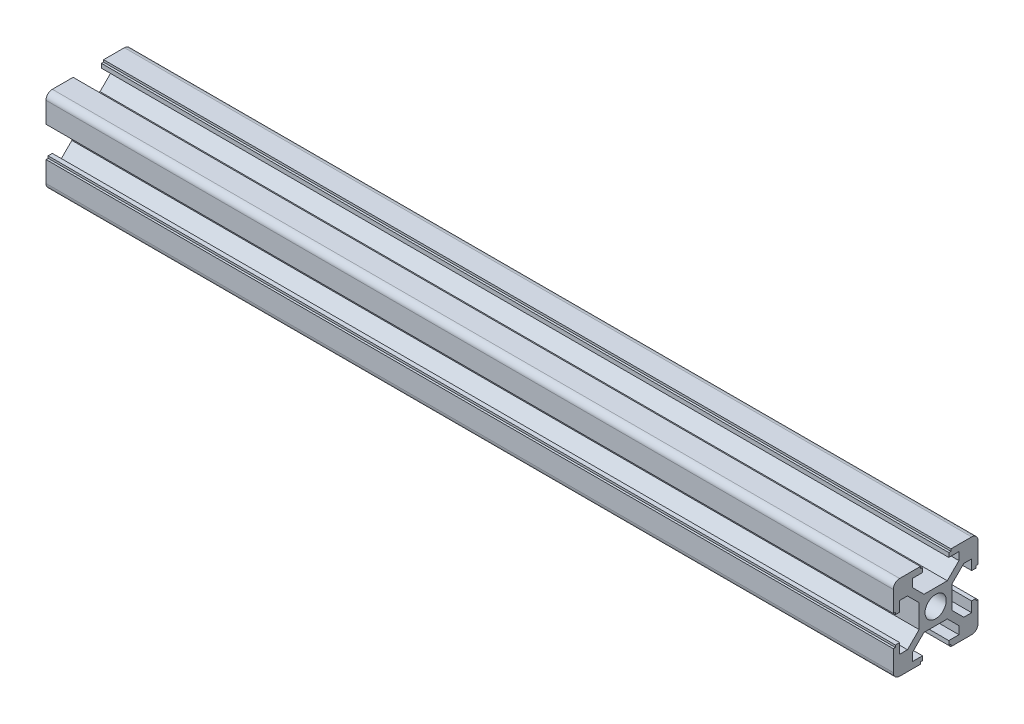
SolidWorks part; units mm, degrees
ref_plane "前视基准面" through (0, 0, 0) normal (0, 0, 1) x (1, 0, 0)
ref_plane "上视基准面" through (0, 0, 0) normal (0, 1, 0) x (1, 0, 0)
ref_plane "右视基准面" through (0, 0, 0) normal (1, 0, 0) x (0, 0, -1)
other "Configuration Table"
sketch "草图1" plane through (0, 0, 0) normal (0, 1, 0) x (1, 0, 0)
  line L0 (0, 0) -> (200, 0)
  dimension "D1" = 200
other "铝型材 20 X 20 X R1.5(1)"
ref_plane "基准面1" through (0, 0, 0) normal (1, 0, 0) x (0, 0, -1)
sketch "Sketch1" plane through (0, 0, 0) normal (1, 0, 0) x (0, 0, -1)
  line L0 (-3.6, 10) -> (-3.6, 9.5)
  line L1 (-3.6, 9.5) -> (-3.1, 9.5)
  line L2 (-3.1, 9.5) -> (-3.1, 8.5)
  line L3 (-3.1, 8.5) -> (-5.5, 8.5)
  line L4 (-8.5, -10) -> (-3.6, -10)
  line L5 (-10, -8.5) -> (-10, -3.6)
  line L6 (8.5, 10) -> (3.6, 10)
  line L7 (10, 8.5) -> (10, 3.6)
  line L8 (0, 14.8756) -> (0, 0) construction
  line L9 (0, 0) -> (14.1675, 0) construction
  line L10 (-5.5, 8.5) -> (-5.5, 6.65)
  line L11 (-5.5, 6.65) -> (-2.75, 3.9)
  line L12 (-2.75, 3.9) -> (2.75, 3.9)
  line L13 (5.5, 6.65) -> (2.75, 3.9)
  line L14 (5.5, 8.5) -> (5.5, 6.65)
  line L15 (3.1, 8.5) -> (5.5, 8.5)
  line L16 (3.1, 9.5) -> (3.1, 8.5)
  line L17 (3.6, 9.5) -> (3.1, 9.5)
  line L18 (3.6, 10) -> (3.6, 9.5)
  line L19 (-3.6, 10) -> (-8.5, 10)
  line L20 (10, 3.6) -> (9.5, 3.6)
  line L21 (9.5, 3.6) -> (9.5, 3.1)
  line L22 (9.5, 3.1) -> (8.5, 3.1)
  line L23 (8.5, 3.1) -> (8.5, 5.5)
  line L24 (8.5, 5.5) -> (6.65, 5.5)
  line L25 (6.65, 5.5) -> (3.9, 2.75)
  line L26 (3.9, 2.75) -> (3.9, -2.75)
  line L27 (6.65, -5.5) -> (3.9, -2.75)
  line L28 (8.5, -5.5) -> (6.65, -5.5)
  line L29 (8.5, -3.1) -> (8.5, -5.5)
  line L30 (9.5, -3.1) -> (8.5, -3.1)
  line L31 (9.5, -3.6) -> (9.5, -3.1)
  line L32 (10, -3.6) -> (9.5, -3.6)
  line L33 (3.6, -10) -> (3.6, -9.5)
  line L34 (3.6, -9.5) -> (3.1, -9.5)
  line L35 (3.1, -9.5) -> (3.1, -8.5)
  line L36 (3.1, -8.5) -> (5.5, -8.5)
  line L37 (5.5, -8.5) -> (5.5, -6.65)
  line L38 (5.5, -6.65) -> (2.75, -3.9)
  line L39 (2.75, -3.9) -> (-2.75, -3.9)
  line L40 (-5.5, -6.65) -> (-2.75, -3.9)
  line L41 (-5.5, -8.5) -> (-5.5, -6.65)
  line L42 (-3.1, -8.5) -> (-5.5, -8.5)
  line L43 (-3.1, -9.5) -> (-3.1, -8.5)
  line L44 (-3.6, -9.5) -> (-3.1, -9.5)
  line L45 (-3.6, -10) -> (-3.6, -9.5)
  line L46 (-10, -3.6) -> (-9.5, -3.6)
  line L47 (-9.5, -3.6) -> (-9.5, -3.1)
  line L48 (-9.5, -3.1) -> (-8.5, -3.1)
  line L49 (-8.5, -3.1) -> (-8.5, -5.5)
  line L50 (-8.5, -5.5) -> (-6.65, -5.5)
  line L51 (-6.65, -5.5) -> (-3.9, -2.75)
  line L52 (-3.9, -2.75) -> (-3.9, 2.75)
  line L53 (-6.65, 5.5) -> (-3.9, 2.75)
  line L54 (-8.5, 5.5) -> (-6.65, 5.5)
  line L55 (-8.5, 3.1) -> (-8.5, 5.5)
  line L56 (-9.5, 3.1) -> (-8.5, 3.1)
  line L57 (-9.5, 3.6) -> (-9.5, 3.1)
  line L58 (-10, 3.6) -> (-9.5, 3.6)
  line L59 (3.6, -10) -> (8.5, -10)
  line L60 (-10, 3.6) -> (-10, 8.5)
  line L61 (10, -3.6) -> (10, -8.5)
  circle A0 centre (0, 0) radius 2.5
  arc A1 (-10, 8.5) -> (-8.5, 10) centre (-8.5, 8.5) cw
  arc A2 (10, 8.5) -> (8.5, 10) centre (8.5, 8.5) ccw
  arc A3 (-8.5, -10) -> (-10, -8.5) centre (-8.5, -8.5) cw
  arc A4 (8.5, -10) -> (10, -8.5) centre (8.5, -8.5) ccw
  point P0 (-10, 0)
  point P1 (10, 0)
  point P2 (0, 10)
  point P3 (0, -10)
  point P4 (0, 0)
  point P5 (-10, -10)
  point P6 (10, -10)
  point P7 (10, 10)
  point P8 (-10, 10)
  point P13 (0, 0)
  point P36 (-10, 10)
  point P39 (10, 10)
  dimension "D1" = 11
  dimension "D2" = 20
  dimension "D3" = 6.2
  dimension "D4" = 7.2
  dimension "D5" = 6.1
  dimension "D6" = 5
  dimension "D7" = 1.5
  dimension "D8" = 45
  dimension "D9" = 0.5
  dimension "D10" = 1
  dimension "D11" = 5.5
